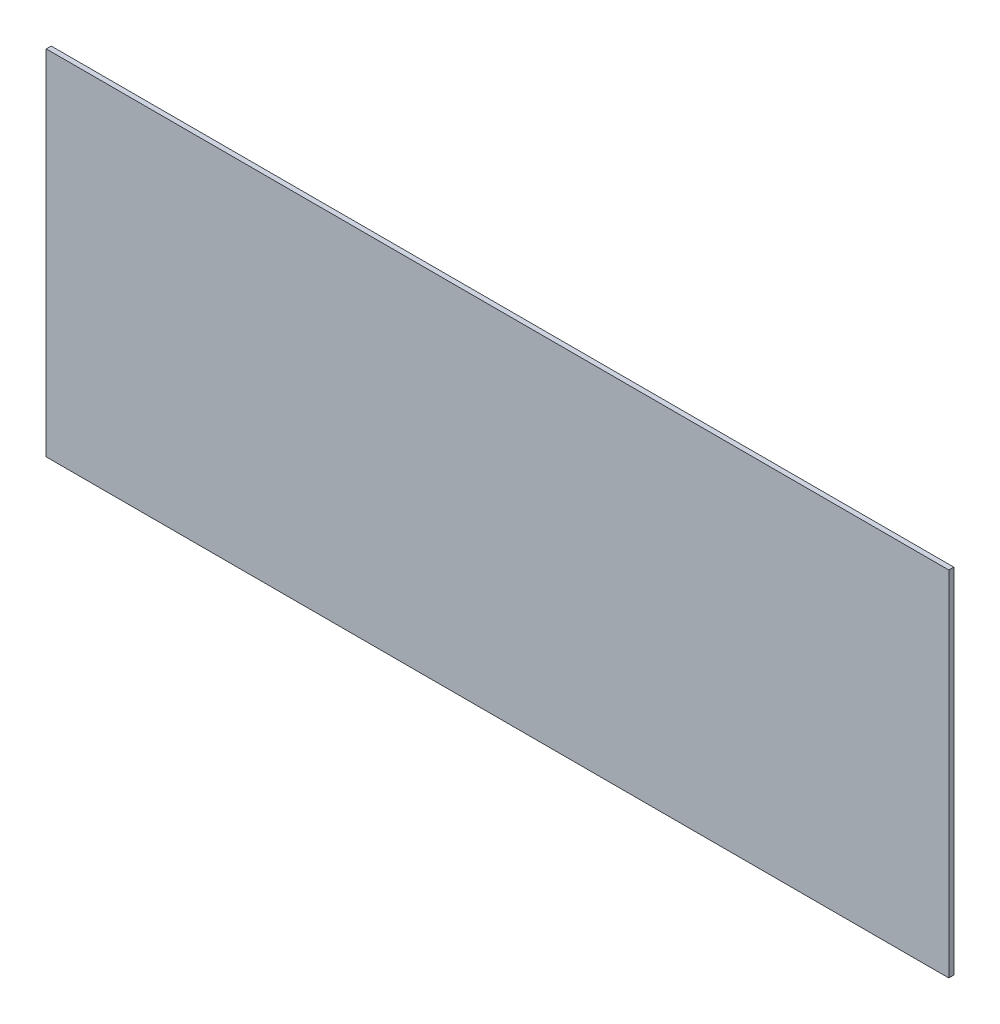
SolidWorks part; units mm, degrees
material "Acrylic (Medium-high impact)"
ref_plane "Front Plane" through (0, 0, 0) normal (0, 0, 1) x (1, 0, 0)
ref_plane "Top Plane" through (0, 0, 0) normal (0, 1, 0) x (1, 0, 0)
ref_plane "Right Plane" through (0, 0, 0) normal (1, 0, 0) x (0, 0, -1)
sketch "Sketch1" plane through (0, 0, 0) normal (0, 0, 1) x (1, 0, 0)
  line L4 (3070.6348, 1129.8017) -> (3093.6428, 1129.8017)
  line L5 (3093.6428, 1129.8017) -> (3093.6428, 1138.8097)
  line L6 (3093.6428, 1138.8097) -> (3070.6348, 1138.8097)
  line L7 (3070.6348, 1138.8097) -> (3070.6348, 1129.8017)
  line L8 (3070.6348, 1129.8017) -> (3093.6428, 1129.8017)
  line L9 (3093.6428, 1129.8017) -> (3093.6428, 1138.8097)
  line L10 (3093.6428, 1138.8097) -> (3070.6348, 1138.8097)
  line L11 (3070.6348, 1138.8097) -> (3070.6348, 1129.8017)
  dimension "D1" = 0
extrude "Boss-Extrude1" add sketch "Sketch1" along normal blind 0.127
